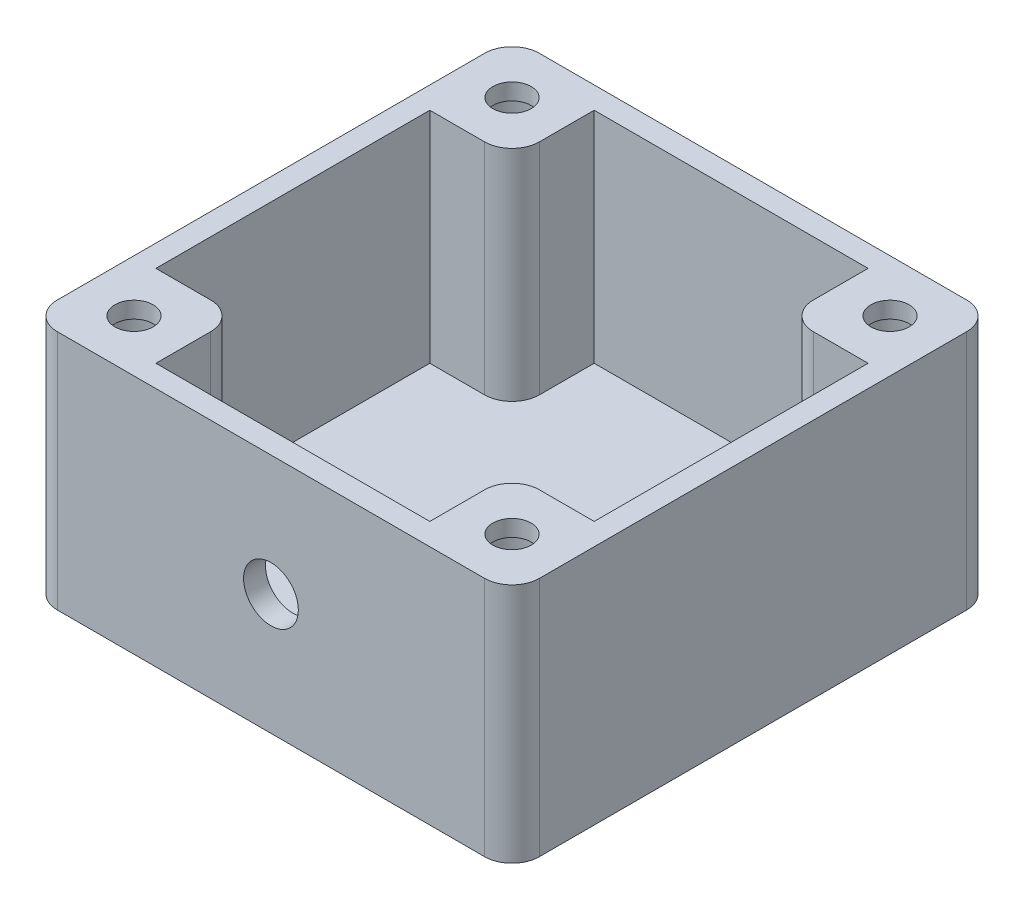
SolidWorks part; units mm, degrees
ref_plane "Front" through (0, 0, 0) normal (0, 0, 1) x (1, 0, 0)
ref_plane "Top" through (0, 0, 0) normal (0, 1, 0) x (1, 0, 0)
ref_plane "Right" through (0, 0, 0) normal (1, 0, 0) x (0, 0, -1)
sketch "Sketch1" plane through (0, 0, 0) normal (0, 1, 0) x (1, 0, 0)
  line L1 (-12.5, -20) -> (12.5, -20)
  line L2 (-12.5, -20) -> (-12.5, 20)
  line L3 (-12.5, 20) -> (12.5, 20)
  line L4 (12.5, -20) -> (12.5, 20)
  line L5 (-12.5, -20) -> (12.5, 20) construction
  line L6 (-12.5, 20) -> (12.5, -20) construction
  line L7 (-22, -22) -> (22, -22)
  line L8 (-22, -22) -> (-22, 22)
  line L9 (-22, 22) -> (22, 22)
  line L10 (22, -22) -> (22, 22)
  line L11 (-22, -22) -> (22, 22) construction
  line L12 (-22, 22) -> (22, -22) construction
  point P0 (0, 0)
  point P10 (0, 0)
  dimension "45" = 40
  dimension "D6" = 25
  dimension "D7" = 9.5
  dimension "D8" = 2
extrude "Boss-Extrude4" add sketch "Sketch1" along normal blind 20
sketch "Sketch4" plane through (0, 0, 0) normal (0, -1, 0) x (1, 0, 0)
  line L1 (22, -22) -> (-22, -22)
  line L2 (22, -22) -> (22, 22)
  line L3 (22, 22) -> (-22, 22)
  line L4 (-22, -22) -> (-22, 22)
  line L5 (22, -22) -> (-22, 22) construction
  line L6 (22, 22) -> (-22, -22) construction
  point P0 (0, 0)
extrude "Boss-Extrude5" add sketch "Sketch4" along normal blind 2
sketch "Sketch5" plane through (0, 0, 0) normal (0, 1, 0) x (1, 0, 0)
  line L1 (0, 0) -> (0, -18.2319) construction
  line L2 (0, 0) -> (-2.9072, -7.9874) construction
  line L3 (-4.3887, -8.222) -> (-1.9632, -9.1531)
  circle A0 centre (0, 0) radius 3.45
  arc A2 (-1.9632, -9.1531) -> (-4.3887, -8.222) centre (-2.9072, -7.9874) ccw
  dimension "D1" = 6.9
  dimension "D3" = 3
  dimension "D2" = 8.5
  dimension "D4" = 20
  dimension "D5" = 0.75
extrude "Cut-Extrude2" cut sketch "Sketch5" against normal blind 2
sketch "Sketch6" plane through (0, 20, 0) normal (0, 1, 0) x (1, 0, 0)
  line L0 (0, 22) -> (0, -22) construction
  line L1 (22, 22) -> (-22, 22) construction
  line L2 (-22, -22) -> (22, -22) construction
  line L3 (-12.5, -20) -> (-22, -20) construction
  line L4 (-22, 22) -> (-22, -22) construction
  line L5 (-17.25, -20) -> (-17.25, 22) construction
  circle A0 centre (-17.25, 17.25) radius 1.75
  circle A1 centre (-17.25, -17.25) radius 1.75
  dimension "D2" = 3.5
  dimension "D1" = 4.75
  dimension "D3" = 4.75
  dimension "D4" = 4.75
extrude "Cut-Extrude3" cut sketch "Sketch6" against normal through all
mirror "Mirror1" about plane through (0, 0, 0) normal (1, 0, 0) of "Cut-Extrude3"
sketch "Sketch7" plane through (0, -2, 0) normal (0, -1, 0) x (1, 0, 0)
  circle A0 centre (-17.25, 17.25) radius 3.25
  circle A1 centre (17.25, 17.25) radius 3.25
  circle A2 centre (17.25, -17.25) radius 3.25
  circle A3 centre (-17.25, -17.25) radius 3.25
  point P11 (-17.25, -17.25)
  point P13 (-17.25, -17.25)
  point P14 (-17.25, -17.25)
  point P15 (-18.5, -18.5)
  point P16 (0, 0)
  point P17 (0, 0)
  point P18 (-22.25, -22.25)
  point P20 (0, 0)
  point P21 (0, 0)
  dimension "D1" = 6.5
extrude "Cut-Extrude4" cut sketch "Sketch7" against normal offset from surface (20.5 mm away) 1.5 up to face at (17.25, 20, -15.5)
sketch "Sketch10" plane through (0, 20, 0) normal (0, 1, 0) x (1, 0, 0)
  line L0 (-12.5, 20) -> (-12.5, -20) construction
  line L1 (-12.5, 12.5) -> (-20, 12.5)
  line L2 (-12.5, 12.5) -> (-12.5, -12.5)
  line L3 (-12.5, -12.5) -> (-20, -12.5)
  line L4 (-20, 12.5) -> (-20, -12.5)
  line L5 (-22, 22) -> (-22, -22) construction
  line L7 (-22, 22) -> (22, 22) construction
  line L8 (12.5, 20) -> (-12.5, 20) construction
  circle A0 centre (-17.25, 17.25) radius 1.75 construction
  circle A1 centre (-17.25, -17.25) radius 1.75 construction
  dimension "D3" = 4.75
  dimension "D1" = 2
  dimension "D2" = 2
  dimension "D4" = 4.75
  dimension "D5" = 4.75
extrude "Cut-Extrude5" cut sketch "Sketch10" against normal up to surface (20 mm away) up to face at (0, 0, 3.45)
mirror "Mirror2" about plane through (0, 0, 0) normal (1, 0, 0) of "Cut-Extrude5"
sketch "Sketch11" plane through (0, 0, 22) normal (0, 0, 1) x (1, 0, 0)
  line L0 (-22, 9) -> (22, 9) construction
  line L1 (-22, 20) -> (-22, -2) construction
  line L2 (22, 20) -> (22, -2) construction
  circle A0 centre (0, 9) radius 2.5
  dimension "D1" = 5
extrude "Cut-Extrude6" cut sketch "Sketch11" against normal up to next
fillet "Fillet1" radius 2.5 8 edges at (-22, 9, 22) (22, 9, 22) (22, 9, -22) (12.5, 10, 12.5) (-12.5, 10, 12.5) (12.5, 10, -12.5) (-12.5, 10, -12.5) (-22, 9, -22)
equation "\"D1@Sketch6\"=\"D3@Sketch6\""
equation "\"D4@Sketch6\"=\"D3@Sketch6\""
equation "\"D1@Sketch10\"=\"D2@Sketch10\""
equation "\"D4@Sketch10\"=\"D3@Sketch10\""
equation "\"D5@Sketch10\"=\"D4@Sketch10\""
equation "\"D7@Sketch1\" =  ( \"45@Sketch1\" + 2 * \"D8@Sketch1\" - \"D6@Sketch1\" )  / 2"
equation "\"D5@Sketch5\"=\"D3@Sketch5\"/4"
